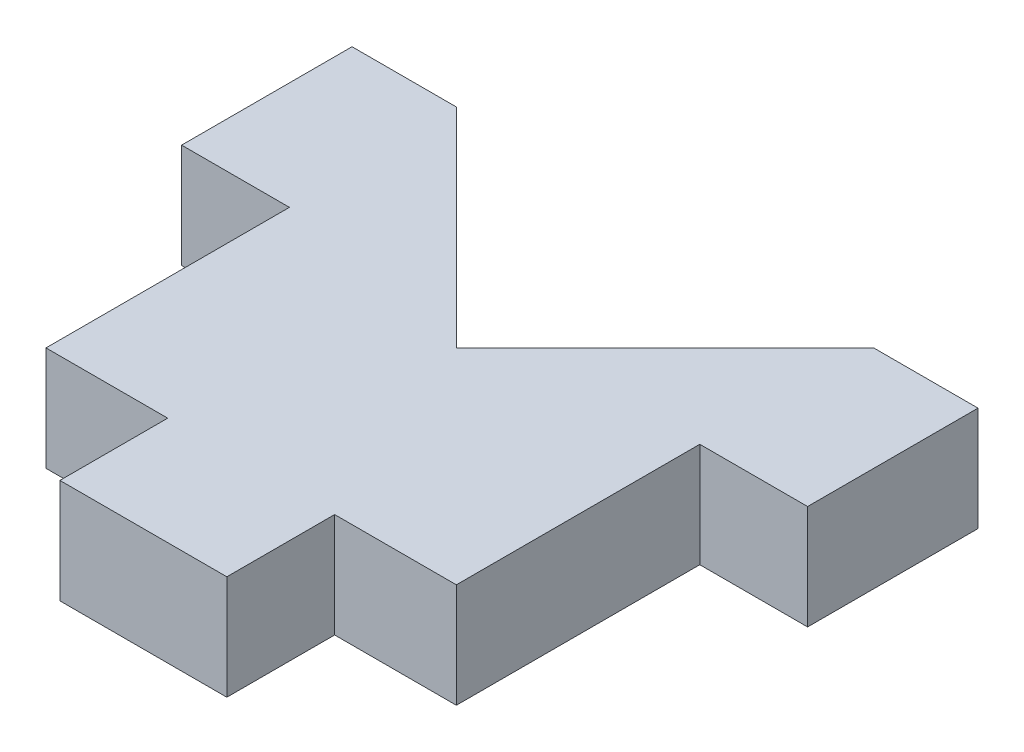
SolidWorks part; units mm, degrees
ref_plane "Front Plane" through (0, 0, 0) normal (0, 0, 1) x (1, 0, 0)
ref_plane "Top Plane" through (0, 0, 0) normal (0, 1, 0) x (1, 0, 0)
ref_plane "Right Plane" through (0, 0, 0) normal (1, 0, 0) x (0, 0, -1)
sketch "Sketch1" plane through (0, 0, 0) normal (0, 1, 0) x (1, 0, 0)
  line L0 (0, 0) -> (0, 15) construction
  line L1 (-9, 3) -> (9, 3) construction
  line L2 (-6, 15) -> (-6, 0) construction
  line L3 (-6, 15) -> (-9, 15)
  line L4 (6, 15) -> (6, 0) construction
  line L5 (6, 15) -> (0, 9) construction
  line L6 (0, 9) -> (-6, 15) construction
  line L7 (6, 15) -> (0, 9)
  line L8 (0, 9) -> (-6, 15)
  line L9 (9, 15) -> (-9, 15) construction
  line L10 (9, 15) -> (9, 0) construction
  line L11 (9, 15) -> (9, 0)
  line L12 (9, 0) -> (-9, 0)
  line L13 (-9, 0) -> (-9, 15)
  line L14 (6, 15) -> (9, 15)
sketch "Sketch2" plane through (0, 0, 0) normal (0, 0, 1) x (1, 0, 0)
  line L0 (0, 0) -> (0, 3) construction
  line L1 (9, 0) -> (-9, 0)
  line L2 (9, 0) -> (9, 3)
  line L3 (9, 3) -> (-9, 3)
  line L4 (-9, 0) -> (-9, 3)
extrude "Boss-Extrude1" add sketch "Sketch1" along normal up to vertex (3 mm away) up to point (9, 3, 0)
sketch "Sketch3" plane through (0, 0, 0) normal (0, 1, 0) x (1, 0, 0)
  line L0 (0, 0) -> (0, 9) construction
  line L2 (9, 0) -> (9, 10)
  line L3 (9, 10) -> (6, 10)
  line L4 (6, 0) -> (6, 10) construction
  line L6 (2.5, 0) -> (2.5, 3)
  line L7 (-9, 15) -> (-9, 0)
  line L8 (-6, 15) -> (-9, 15)
  line L9 (0, 9) -> (-6, 15)
  line L10 (6, 15) -> (0, 9)
  line L11 (9, 15) -> (6, 15)
  line L12 (9, 0) -> (9, 15)
  line L13 (-9, 0) -> (9, 0)
  line L14 (-9, 15) -> (-9, 0) construction
  line L16 (0, 9) -> (-6, 15) construction
  line L17 (6, 15) -> (0, 9) construction
  line L18 (9, 15) -> (6, 15) construction
  line L19 (9, 0) -> (9, 15) construction
  line L20 (-9, 0) -> (9, 0) construction
  line L21 (2.5, 3) -> (-2.5, 3) construction
  line L23 (6, 15) -> (6, 0) construction
  line L24 (-9, 3) -> (9, 3) construction
  line L33 (9, 0) -> (2.5, 0)
  line L34 (2.5, 3) -> (6, 3)
  line L35 (6, 3) -> (6, 10)
  line L36 (-9, 0) -> (-2.5, 0)
  line L37 (-9, 0) -> (-9, 10)
  line L38 (-9, 10) -> (-6, 10)
  line L39 (-6, 3) -> (-6, 10)
  line L40 (-2.5, 3) -> (-6, 3)
  line L41 (-2.5, 0) -> (-2.5, 3)
  dimension "D1" = 0
sketch "Sketch6" plane through (0, 0, 0) normal (0, 1, 0) x (1, 0, 0)
  line L0 (-5.9, 3.1) -> (-5.9, 10.1)
  line L1 (-5.9, 10.1) -> (-9.1, 10.1)
  line L2 (-9.1, 10.1) -> (-9.1, -0.1)
  line L3 (-9.1, -0.1) -> (-2.4, -0.1)
  line L4 (-2.4, -0.1) -> (-2.4, 3.1)
  line L5 (-2.4, 3.1) -> (-5.9, 3.1)
  line L6 (-6, 3) -> (-6, 10)
  line L7 (-2.5, 3) -> (-6, 3)
  line L8 (-2.5, 0) -> (-2.5, 3)
  line L9 (-9, 0) -> (-2.5, 0)
  line L10 (-9, 10) -> (-9, 0)
  line L11 (-6, 10) -> (-9, 10)
  line L12 (-6, 3) -> (-6, 10) construction
  line L13 (-2.5, 3) -> (-6, 3) construction
  line L14 (-2.5, 0) -> (-2.5, 3) construction
  line L15 (-9, 0) -> (-2.5, 0) construction
  line L16 (-9, 10) -> (-9, 0) construction
  line L17 (-6, 10) -> (-9, 10) construction
  line L18 (9, 10) -> (6, 10)
  line L19 (9, 0) -> (9, 10)
  line L20 (2.5, 0) -> (9, 0)
  line L21 (2.5, 3) -> (2.5, 0)
  line L22 (6, 3) -> (2.5, 3)
  line L23 (6, 10) -> (6, 3)
  line L24 (9, 10) -> (6, 10) construction
  line L25 (9, 0) -> (9, 10) construction
  line L26 (2.5, 0) -> (9, 0) construction
  line L27 (2.5, 3) -> (2.5, 0) construction
  line L28 (6, 3) -> (2.5, 3) construction
  line L29 (6, 10) -> (6, 3) construction
  line L30 (9.1, 10.1) -> (5.9, 10.1)
  line L31 (5.9, 10.1) -> (5.9, 3.1)
  line L32 (5.9, 3.1) -> (2.4, 3.1)
  line L33 (2.4, 3.1) -> (2.4, -0.1)
  line L34 (2.4, -0.1) -> (9.1, -0.1)
  line L35 (9.1, -0.1) -> (9.1, 10.1)
  dimension "D1" = 0
  dimension "D2" = 0
  dimension "D3" = 0.1
extrude "Cut-Extrude3" cut sketch "Sketch6" along normal through all
